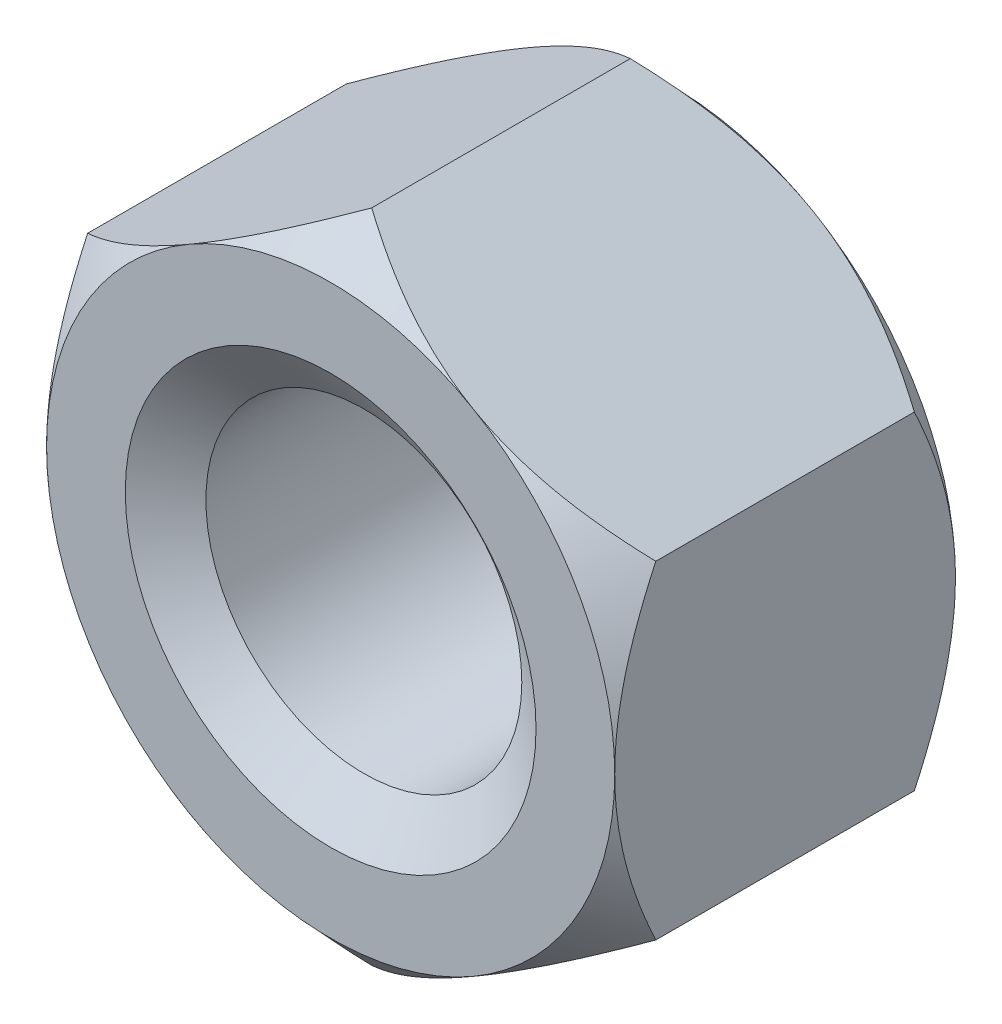
SolidWorks part; units mm, degrees
extrude "BaseNut" add sketch "BaseNutSke" against normal blind 8.5598
sketch "BaseNutSke" plane through (0, 0, 0) normal (0, 0, 1) x (1, 0, 0)
  line L6 (7.1374, 4.1208) -> (7.1374, -4.1208)
  line L7 (-7.1374, 4.1208) -> (-7.1374, -4.1208)
  line L8 (7.1374, 4.1208) -> (0, 8.2416)
  line L9 (0, 8.2416) -> (-7.1374, 4.1208)
  line L10 (-7.1374, -4.1208) -> (0, -8.2416)
  line L11 (0, -8.2416) -> (7.1374, -4.1208)
  circle A0 centre (0, 0) radius 3.9688
  dimension "D1" = 120
cosmetic thread "ThreadCosmetic" parameters "Thread_major"=10.32
pattern_linear "ThdSchPat" [suppressed]
revolve "ThreadSchematic" [suppressed] cut sketch "ThdSchSke" angle 360 about L6
sketch "ThdSchSke" plane through (0, 0, 0) normal (0, 1, 0) x (1, 0, 0)
  line L0 (-5.16, 0.0254) -> (-3.9688, 0.8595)
  line L1 (-3.9688, 0.8595) -> (-1.9844, 0.8595)
  line L2 (-1.9844, 0.8595) -> (-1.9844, -0.8087)
  line L3 (-1.9844, -0.8087) -> (-3.9688, -0.8087)
  line L4 (-3.9688, -0.8087) -> (-5.16, 0.0254)
  line L5 (-3.175, 1.5875) -> (3.175, 1.5875) construction
  line L6 (0, 1.5875) -> (0, -2.9874) construction
  line L7 (0, 7.7003) -> (0, 0.8341) construction
  dimension "SideAngle" = 55
  dimension "D1" = 0.0254
material "Alloy Steel"
ref_plane "Plane1" through (0, 0, 0) normal (0, 0, 1) x (1, 0, 0)
ref_plane "Plane2" through (0, 0, 0) normal (0, 1, 0) x (1, 0, 0)
ref_plane "Plane3" through (0, 0, 0) normal (1, 0, 0) x (0, 0, -1)
sketch "Sketch4" plane through (0, 0, 0) normal (1, 0, 0) x (0, 0, -1)
  line L0 (8.5598, 7.1374) -> (8.1534, 7.1374)
  line L1 (8.5598, 7.1374) -> (8.5598, 20.9416)
  line L2 (8.1534, 20.9416) -> (8.5598, 20.9416)
  line L3 (8.1534, 20.9416) -> (8.1534, 7.1374)
  line L4 (0, 0) -> (34.925, 0) construction
  line L6 (8.5598, 4.1208) -> (8.5598, 8.2416) construction
  line L7 (0, 7.1374) -> (-12.7, 7.1374)
  line L8 (0, 4.1208) -> (0, 8.2416) construction
  line L9 (1.032, 8.2416) -> (1.032, 20.9416)
  line L10 (1.032, 20.9416) -> (-12.7, 20.9416)
  line L11 (-12.7, 20.9416) -> (-12.7, 7.1374)
  line L12 (0, 7.1374) -> (1.032, 8.2416)
  line L14 (0, 4.1208) -> (0, -4.1208) construction
  line L15 (8.5598, 8.2416) -> (0, 8.2416) construction
  dimension "D3" = 12.7
  dimension "D4" = 12.7
revolve "Bearing-Face" [suppressed] cut sketch "Sketch4" angle 360 about L4
sketch "Sketch3" plane through (0, 0, 0) normal (1, 0, 0) x (0, 0, -1)
  line L0 (8.5598, 7.1374) -> (7.5278, 8.2416)
  line L1 (7.5278, 8.2416) -> (7.5278, 20.9416)
  line L2 (7.5278, 20.9416) -> (21.2598, 20.9416)
  line L3 (21.2598, 20.9416) -> (21.2598, 7.1374)
  line L4 (21.2598, 7.1374) -> (8.5598, 7.1374)
  line L5 (8.5598, 4.1208) -> (8.5598, 8.2416) construction
  line L6 (8.5598, 8.2416) -> (0, 8.2416) construction
  line L7 (0, 0) -> (38.6776, 0) construction
  line L8 (8.5598, 0) -> (0, 0) construction
  line L9 (4.2799, 8.2416) -> (4.2799, 44.222) construction
  line L10 (1.032, 20.9416) -> (-12.7, 20.9416)
  line L11 (-12.7, 20.9416) -> (-12.7, 7.1374)
  line L12 (-12.7, 7.1374) -> (0, 7.1374)
  line L13 (0, 7.1374) -> (1.032, 8.2416)
  line L14 (1.032, 8.2416) -> (1.032, 20.9416)
  line L16 (8.5598, 8.2416) -> (0, 8.2416) construction
  dimension "D4" = 12.7
  dimension "D3" = 12.7
revolve "Double-Chamfer" cut sketch "Sketch3" angle 360 about L7
sketch "Sketch5" plane through (0, 0, 0) normal (1, 0, 0) x (0, 0, -1)
  line L0 (8.5344, 5.16) -> (7.6169, 3.8496)
  line L1 (8.5852, 5.16) -> (8.5344, 5.16)
  line L2 (8.5852, 5.16) -> (8.5852, 3.8496)
  line L3 (8.5852, 3.8496) -> (7.6169, 3.8496)
  line L6 (-0.0508, 5.16) -> (0, 5.16)
  line L7 (0, 5.16) -> (0.9175, 3.8496)
  line L9 (0.9175, 3.8496) -> (-0.0508, 3.8496)
  line L10 (-0.0508, 3.8496) -> (-0.0508, 5.16)
  line L11 (25.0375, 0) -> (38.388, 0) construction
  line L12 (8.5598, 0) -> (0, 0) construction
  dimension "D1" = 35
  dimension "D2" = 0.0508
revolve "EndChamfer" cut sketch "Sketch5" angle 360 about L11
equation "\"D2@BaseNutSke\" = \"Width_flats@BaseNutSke\" / 2"
equation "\"D3@BaseNutSke\" = \"Width_flats@BaseNutSke\" / 2"
equation "\"D1@Sketch3\" = \"Width_flats@BaseNutSke\" /2"
equation "\"D2@Sketch3\" = \"Thread_major@ThreadCosmetic\" *.1"
equation "\"D1@Sketch4\" = \"D2@BaseNutSke\""
equation "\"D2@Sketch4\" = \"Thread_major@ThreadCosmetic\" *.10"
equation "\"D4@BaseNutSke\" = \"D3@BaseNutSke\""
equation "\"Thread_major@ThdSchSke\" = \"Thread_major@ThreadCosmetic\""
equation "\"Tap_Drill@ThdSchSke\" = \"Tap_drill@BaseNutSke\""
equation "\"OverCut@ThdSchSke\" = \"Tap_Drill@ThdSchSke\" * 0.5"
equation "\"Num_threads@ThdSchPat\" = int(  ( \"Thickness@BaseNut\" - 0.002 ) / \"Advance@ThdSchSke\" + 0.999 )  + 1"
equation "\"Advance@ThdSchPat\" = ( \"Thickness@BaseNut\" - 0.002 ) /  (\"Num_threads@ThdSchPat\" - 1) 'relax it"
equation "' \"Num_threads@ThdSchPat\" = \"Num_threads@ThdSchPat\" - sgn( \"Num_threads@ThdSchPat\" - 1) '---chamfered tips only---"
equation "\"ThreadMajor@Sketch5\" = \"Thread_major@ThreadCosmetic\" * 0.5"
equation "\"ChamferDepth@Sketch5\" = (\"Thread_major@ThreadCosmetic\" - \"Tap_drill@BaseNutSke\") * 0.55"
equation "\"Offset1@Sketch5\" = \"Thickness@BaseNut\" + 0.001"
equation "\"Offset2@Sketch5\" = \"Offset1@Sketch5\" + 0.002"
